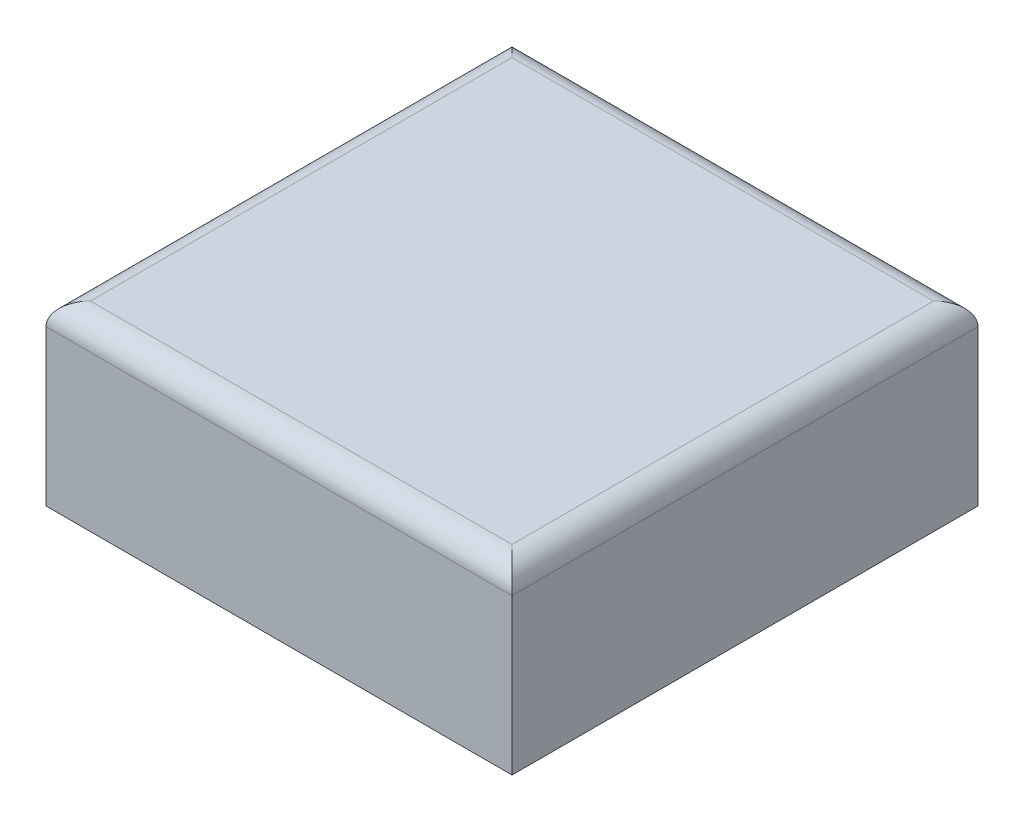
SolidWorks part; units mm, degrees
ref_plane "Front Plane" through (0, 0, 0) normal (0, 0, 1) x (1, 0, 0)
ref_plane "Top Plane" through (0, 0, 0) normal (0, 1, 0) x (1, 0, 0)
ref_plane "Right Plane" through (0, 0, 0) normal (1, 0, 0) x (0, 0, -1)
sketch "Sketch1" plane through (0, 0, 0) normal (0, 1, 0) x (1, 0, 0)
  line L1 (-10.5, 10.5) -> (10.5, 10.5)
  line L2 (-10.5, 10.5) -> (-10.5, -10.5)
  line L3 (-10.5, -10.5) -> (10.5, -10.5)
  line L4 (10.5, 10.5) -> (10.5, -10.5)
  line L5 (0, -10.5) -> (0, 10.5) construction
  line L6 (-10.5, 0) -> (10.5, 0) construction
  point P0 (0, 0)
  dimension "D1" = 21
  dimension "D2" = 21
extrude "Boss-Extrude1" add sketch "Sketch1" along normal blind 8
fillet "Fillet1" radius 1 4 edges at (-10.5, 8, 0) (0, 8, -10.5) (10.5, 8, 0) (0, 8, 10.5)
